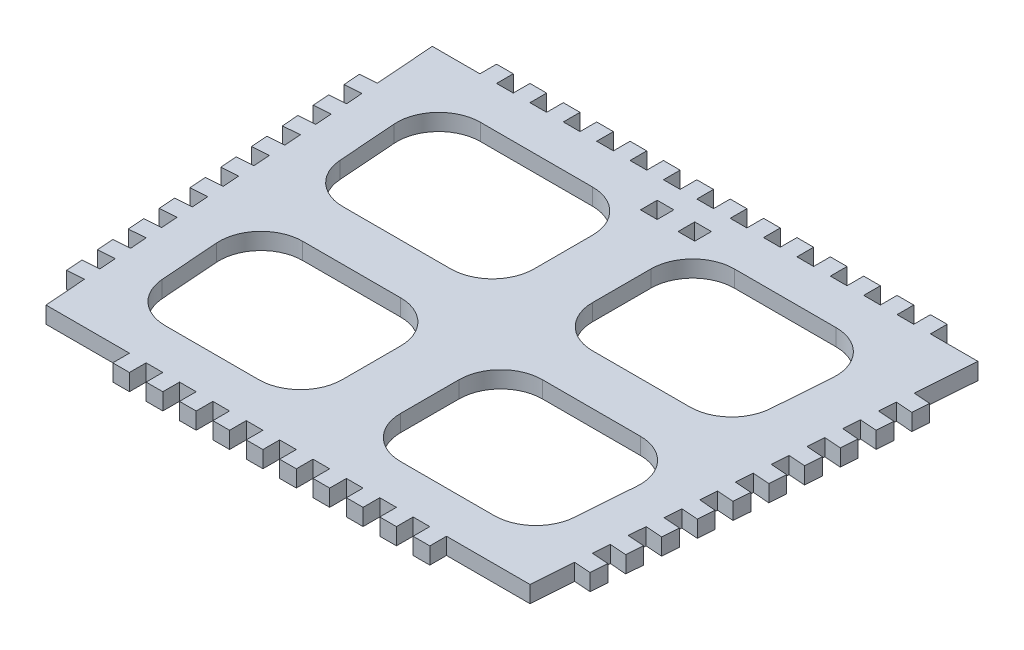
SolidWorks part; units mm, degrees
material "Cedar"
ref_plane "Front Plane" through (0, 0, 0) normal (0, 0, 1) x (1, 0, 0)
ref_plane "Top Plane" through (0, 0, 0) normal (0, 1, 0) x (1, 0, 0)
ref_plane "Right Plane" through (0, 0, 0) normal (1, 0, 0) x (0, 0, -1)
sketch "Sketch1" plane through (0, 0, 0) normal (0, 1, 0) x (1, 0, 0)
  line L0 (-65.4, 43.0243) -> (0, 43.0243)
  line L1 (65.4, 43.0243) -> (58, -56.9757)
  line L2 (58, -56.9757) -> (0, -56.9757)
  line L3 (-58, -56.9757) -> (-65.4, 43.0243)
  line L4 (0, 43.0243) -> (0, -56.9757) construction
  line L5 (0, -6.9757) -> (15.9946, -6.9757) construction
  line L48 (0, -56.9757) -> (-58, -56.9757)
  line L49 (0, 43.0243) -> (65.4, 43.0243)
  dimension "D1" = 100
  dimension "D2" = 65.4
  dimension "D3" = 58
  dimension "D14" = 65.4
  dimension "D15" = 58
extrude "Boss-Extrude1" add sketch "Sketch1" along normal blind 4
sketch "Sketch2" plane through (0, 4, 0) normal (0, 1, 0) x (1, 0, 0)
  line L0 (-65.4, 43.0243) -> (0, 43.0243) construction
  line L1 (-2, 43.0243) -> (-6, 43.0243)
  line L2 (-2, 43.0243) -> (-2, 47.0243)
  line L3 (-2, 47.0243) -> (-6, 47.0243)
  line L4 (-6, 43.0243) -> (-6, 47.0243)
  line L5 (0, 43.0243) -> (0, -56.9757) construction
  line L6 (-10, 43.0243) -> (-14, 43.0243)
  line L7 (-10, 43.0243) -> (-10, 47.0243)
  line L8 (-10, 47.0243) -> (-14, 47.0243)
  line L9 (-14, 43.0243) -> (-14, 47.0243)
  line L10 (-18, 43.0243) -> (-22, 43.0243)
  line L11 (-18, 43.0243) -> (-18, 47.0243)
  line L12 (-18, 47.0243) -> (-22, 47.0243)
  line L13 (-22, 43.0243) -> (-22, 47.0243)
  line L14 (-26, 43.0243) -> (-30, 43.0243)
  line L15 (-26, 43.0243) -> (-26, 47.0243)
  line L16 (-26, 47.0243) -> (-30, 47.0243)
  line L17 (-30, 43.0243) -> (-30, 47.0243)
  line L18 (-34, 43.0243) -> (-38, 43.0243)
  line L19 (-34, 43.0243) -> (-34, 47.0243)
  line L20 (-34, 47.0243) -> (-38, 47.0243)
  line L21 (-38, 43.0243) -> (-38, 47.0243)
  line L22 (-42, 43.0243) -> (-46, 43.0243)
  line L23 (-42, 43.0243) -> (-42, 47.0243)
  line L24 (-42, 47.0243) -> (-46, 47.0243)
  line L25 (-46, 43.0243) -> (-46, 47.0243)
  line L26 (-50, 43.0243) -> (-54, 43.0243)
  line L27 (-50, 43.0243) -> (-50, 47.0243)
  line L28 (-50, 47.0243) -> (-54, 47.0243)
  line L29 (-54, 43.0243) -> (-54, 47.0243)
  line L30 (0, 43.0243) -> (0, 11.5799) construction
  line L31 (54, 43.0243) -> (54, 47.0243)
  line L32 (50, 47.0243) -> (54, 47.0243)
  line L33 (50, 43.0243) -> (50, 47.0243)
  line L34 (50, 43.0243) -> (54, 43.0243)
  line L35 (46, 43.0243) -> (46, 47.0243)
  line L36 (42, 47.0243) -> (46, 47.0243)
  line L37 (42, 43.0243) -> (42, 47.0243)
  line L38 (42, 43.0243) -> (46, 43.0243)
  line L39 (38, 43.0243) -> (38, 47.0243)
  line L40 (34, 47.0243) -> (38, 47.0243)
  line L41 (34, 43.0243) -> (34, 47.0243)
  line L42 (34, 43.0243) -> (38, 43.0243)
  line L43 (30, 43.0243) -> (30, 47.0243)
  line L44 (26, 47.0243) -> (30, 47.0243)
  line L45 (26, 43.0243) -> (26, 47.0243)
  line L46 (26, 43.0243) -> (30, 43.0243)
  line L47 (22, 43.0243) -> (22, 47.0243)
  line L48 (18, 47.0243) -> (22, 47.0243)
  line L49 (18, 43.0243) -> (18, 47.0243)
  line L50 (18, 43.0243) -> (22, 43.0243)
  line L51 (14, 43.0243) -> (14, 47.0243)
  line L52 (10, 47.0243) -> (14, 47.0243)
  line L53 (10, 43.0243) -> (10, 47.0243)
  line L54 (10, 43.0243) -> (14, 43.0243)
  line L55 (6, 43.0243) -> (6, 47.0243)
  line L56 (2, 47.0243) -> (6, 47.0243)
  line L57 (2, 43.0243) -> (2, 47.0243)
  line L58 (2, 43.0243) -> (6, 43.0243)
  line L59 (0, -56.9757) -> (-58, -56.9757) construction
  line L60 (-6, -56.9757) -> (-2, -56.9757)
  line L61 (-6, -56.9757) -> (-6, -60.9757)
  line L62 (-6, -60.9757) -> (-2, -60.9757)
  line L63 (-2, -56.9757) -> (-2, -60.9757)
  line L64 (-14, -56.9757) -> (-10, -56.9757)
  line L65 (-14, -56.9757) -> (-14, -60.9757)
  line L66 (-14, -60.9757) -> (-10, -60.9757)
  line L67 (-10, -56.9757) -> (-10, -60.9757)
  line L68 (-22, -56.9757) -> (-18, -56.9757)
  line L69 (-22, -56.9757) -> (-22, -60.9757)
  line L70 (-22, -60.9757) -> (-18, -60.9757)
  line L71 (-18, -56.9757) -> (-18, -60.9757)
  line L72 (-30, -56.9757) -> (-26, -56.9757)
  line L73 (-30, -56.9757) -> (-30, -60.9757)
  line L74 (-30, -60.9757) -> (-26, -60.9757)
  line L75 (-26, -56.9757) -> (-26, -60.9757)
  line L76 (-38, -56.9757) -> (-34, -56.9757)
  line L77 (-38, -56.9757) -> (-38, -60.9757)
  line L78 (-38, -60.9757) -> (-34, -60.9757)
  line L79 (-34, -56.9757) -> (-34, -60.9757)
  line L80 (34, -56.9757) -> (34, -60.9757)
  line L81 (38, -60.9757) -> (34, -60.9757)
  line L82 (38, -56.9757) -> (38, -60.9757)
  line L83 (38, -56.9757) -> (34, -56.9757)
  line L84 (26, -56.9757) -> (26, -60.9757)
  line L85 (30, -60.9757) -> (26, -60.9757)
  line L86 (30, -56.9757) -> (30, -60.9757)
  line L87 (30, -56.9757) -> (26, -56.9757)
  line L88 (18, -56.9757) -> (18, -60.9757)
  line L89 (22, -60.9757) -> (18, -60.9757)
  line L90 (22, -56.9757) -> (22, -60.9757)
  line L91 (22, -56.9757) -> (18, -56.9757)
  line L92 (10, -56.9757) -> (10, -60.9757)
  line L93 (14, -60.9757) -> (10, -60.9757)
  line L94 (14, -56.9757) -> (14, -60.9757)
  line L95 (14, -56.9757) -> (10, -56.9757)
  line L96 (2, -56.9757) -> (2, -60.9757)
  line L97 (6, -60.9757) -> (2, -60.9757)
  line L98 (6, -56.9757) -> (6, -60.9757)
  line L99 (6, -56.9757) -> (2, -56.9757)
  dimension "D1" = 4
  dimension "D2" = 2
  dimension "D3" = 4
  dimension "D4" = 2
  dimension "D5" = 4
  dimension "D6" = 4
extrude "Boss-Extrude2" add sketch "Sketch2" against normal blind 4
sketch "Sketch4" plane through (0, 4, 0) normal (0, 1, 0) x (1, 0, 0)
  line L0 (-53.838, 22.2864) -> (-52.802, 8.2864)
  line L1 (-42.8293, -0.9757) -> (-17, -0.9757)
  line L2 (-7, 9.0243) -> (-7, 23.0243)
  line L3 (-17, 33.0243) -> (-43.8653, 33.0243)
  line L5 (-58, -56.9757) -> (-65.4, 43.0243) construction
  line L6 (0, -56.9757) -> (-58, -56.9757) construction
  line L7 (-65.4, 43.0243) -> (0, 43.0243) construction
  line L8 (0, 43.0243) -> (0, -56.9757) construction
  line L9 (0, 43.0243) -> (65.4, 43.0243) construction
  line L10 (7, 23.0243) -> (7, 9.0243)
  line L11 (-6.5, 38.0243) -> (-2.5, 38.0243)
  line L12 (17, -0.9757) -> (40.3576, -0.9757)
  line L13 (50.3304, 8.2864) -> (51.3664, 22.2864)
  line L14 (41.3936, 33.0243) -> (17, 33.0243)
  line L15 (65.4, 43.0243) -> (58, -56.9757) construction
  line L16 (0, -6.9757) -> (15.9946, -6.9757) construction
  line L17 (0, -6.9757) -> (17.2564, -6.9757) construction
  line L18 (-50.434, -23.7136) -> (-49.398, -37.7136)
  line L19 (-39.4253, -46.9757) -> (-17, -46.9757)
  line L20 (-7, -36.9757) -> (-7, -22.9757)
  line L21 (-17, -12.9757) -> (-40.4613, -12.9757)
  line L22 (7, -22.9757) -> (7, -36.9757)
  line L23 (17, -46.9757) -> (39.4253, -46.9757)
  line L24 (49.398, -37.7136) -> (50.434, -23.7136)
  line L25 (40.4613, -12.9757) -> (17, -12.9757)
  line L26 (-6.5, 38.0243) -> (-6.5, 34.0243)
  line L27 (-6.5, 34.0243) -> (-2.5, 34.0243)
  line L28 (-2.5, 38.0243) -> (-2.5, 34.0243)
  line L29 (2.5, 38.0243) -> (6.5, 38.0243)
  line L30 (2.5, 38.0243) -> (2.5, 34.0243)
  line L31 (2.5, 34.0243) -> (6.5, 34.0243)
  line L32 (6.5, 38.0243) -> (6.5, 34.0243)
  arc A0 (-52.802, 8.2864) -> (-42.8293, -0.9757) centre (-42.8293, 9.0243) ccw
  arc A1 (-17, -0.9757) -> (-7, 9.0243) centre (-17, 9.0243) ccw
  arc A2 (-7, 23.0243) -> (-17, 33.0243) centre (-17, 23.0243) ccw
  arc A3 (-53.838, 22.2864) -> (-43.8653, 33.0243) centre (-43.8653, 23.0243) cw
  arc A4 (7, 9.0243) -> (17, -0.9757) centre (17, 9.0243) ccw
  arc A5 (40.3576, -0.9757) -> (50.3304, 8.2864) centre (40.3576, 9.0243) ccw
  arc A6 (51.3664, 22.2864) -> (41.3936, 33.0243) centre (41.3936, 23.0243) ccw
  arc A7 (7, 23.0243) -> (17, 33.0243) centre (17, 23.0243) cw
  arc A8 (-49.398, -37.7136) -> (-39.4253, -46.9757) centre (-39.4253, -36.9757) ccw
  arc A9 (-17, -46.9757) -> (-7, -36.9757) centre (-17, -36.9757) ccw
  arc A10 (-7, -22.9757) -> (-17, -12.9757) centre (-17, -22.9757) ccw
  arc A11 (-50.434, -23.7136) -> (-40.4613, -12.9757) centre (-40.4613, -22.9757) cw
  arc A12 (7, -36.9757) -> (17, -46.9757) centre (17, -36.9757) ccw
  arc A13 (39.4253, -46.9757) -> (49.398, -37.7136) centre (39.4253, -36.9757) ccw
  arc A14 (50.434, -23.7136) -> (40.4613, -12.9757) centre (40.4613, -22.9757) ccw
  arc A15 (7, -22.9757) -> (17, -12.9757) centre (17, -22.9757) cw
  dimension "D1" = 10
  dimension "D5" = 10
  dimension "D6" = 10
  dimension "D8" = 10
  dimension "D10" = 10
  dimension "D2" = 6
  dimension "D3" = 7
  dimension "D4" = 10
  dimension "D7" = 10
  dimension "D9" = 7
  dimension "D11" = 10
  dimension "D12" = 7
  dimension "D13" = 7
  dimension "D14" = 10
  dimension "D15" = 6
  dimension "D16" = 10
  dimension "D17" = 4
  dimension "D18" = 4
  dimension "D19" = 2.5
  dimension "D20" = 4
  dimension "D21" = 4
  dimension "D22" = 2.5
  dimension "D23" = 5
extrude "Cut-Extrude1" cut sketch "Sketch4" against normal blind 10
sketch "Sketch5" plane through (0, 4, 0) normal (0, 1, 0) x (1, 0, 0)
  line L0 (-65.4, 43.0243) -> (-58, -56.9757) construction
  line L1 (-61.7, -6.9757) -> (61.7, -6.9757) construction
  line L2 (65.4, 43.0243) -> (58, -56.9757) construction
  line L3 (0, -6.9757) -> (0, -56.9757) construction
  line L4 (-59.6236, -35.0357) -> (-63.6127, -35.3308)
  line L5 (-63.6127, -35.3308) -> (-63.3175, -39.3199)
  line L6 (-63.3175, -39.3199) -> (-59.3284, -39.0247)
  line L7 (-59.3284, -39.0247) -> (-59.6236, -35.0357)
  line L8 (-61.7, -6.9757) -> (-78.3114, -8.2049) construction
  line L9 (-59.0332, -43.0138) -> (-63.0223, -43.309)
  line L10 (-63.0223, -43.309) -> (-62.7271, -47.2981)
  line L11 (-62.7271, -47.2981) -> (-58.738, -47.0029)
  line L12 (-58.738, -47.0029) -> (-59.0332, -43.0138)
  line L13 (-60.2139, -27.0575) -> (-64.203, -27.3527)
  line L14 (-64.203, -27.3527) -> (-63.9078, -31.3418)
  line L15 (-63.9078, -31.3418) -> (-59.9188, -31.0466)
  line L16 (-59.9188, -31.0466) -> (-60.2139, -27.0575)
  line L17 (-60.8043, -19.0793) -> (-64.7934, -19.3745)
  line L18 (-64.7934, -19.3745) -> (-64.4982, -23.3636)
  line L19 (-64.4982, -23.3636) -> (-60.5091, -23.0684)
  line L20 (-60.5091, -23.0684) -> (-60.8043, -19.0793)
  line L21 (-61.3947, -11.1011) -> (-65.3838, -11.3963)
  line L22 (-65.3838, -11.3963) -> (-65.0886, -15.3854)
  line L23 (-65.0886, -15.3854) -> (-61.0995, -15.0902)
  line L24 (-61.0995, -15.0902) -> (-61.3947, -11.1011)
  line L25 (-61.9851, -3.1229) -> (-65.9742, -3.4181)
  line L26 (-65.9742, -3.4181) -> (-65.679, -7.4072)
  line L27 (-65.679, -7.4072) -> (-61.6899, -7.112)
  line L28 (-61.6899, -7.112) -> (-61.9851, -3.1229)
  line L29 (-62.5755, 4.8553) -> (-66.5646, 4.5601)
  line L30 (-66.5646, 4.5601) -> (-66.2694, 0.571)
  line L31 (-66.2694, 0.571) -> (-62.2803, 0.8662)
  line L32 (-62.2803, 0.8662) -> (-62.5755, 4.8553)
  line L33 (-63.1659, 12.8335) -> (-67.155, 12.5383)
  line L34 (-67.155, 12.5383) -> (-66.8598, 8.5492)
  line L35 (-66.8598, 8.5492) -> (-62.8707, 8.8444)
  line L36 (-62.8707, 8.8444) -> (-63.1659, 12.8335)
  line L37 (-63.7563, 20.8116) -> (-67.7454, 20.5165)
  line L38 (-67.7454, 20.5165) -> (-67.4502, 16.5274)
  line L39 (-67.4502, 16.5274) -> (-63.4611, 16.8226)
  line L40 (-63.4611, 16.8226) -> (-63.7563, 20.8116)
  line L41 (-64.3466, 28.7898) -> (-68.3357, 28.4946)
  line L42 (-68.3357, 28.4946) -> (-68.0405, 24.5055)
  line L43 (-68.0405, 24.5055) -> (-64.0515, 24.8007)
  line L44 (-64.0515, 24.8007) -> (-64.3466, 28.7898)
  line L45 (64.0515, 24.8007) -> (64.3466, 28.7898)
  line L46 (68.0405, 24.5055) -> (64.0515, 24.8007)
  line L47 (68.3357, 28.4946) -> (68.0405, 24.5055)
  line L48 (64.3466, 28.7898) -> (68.3357, 28.4946)
  line L49 (63.4611, 16.8226) -> (63.7563, 20.8116)
  line L50 (67.4502, 16.5274) -> (63.4611, 16.8226)
  line L51 (67.7454, 20.5165) -> (67.4502, 16.5274)
  line L52 (63.7563, 20.8116) -> (67.7454, 20.5165)
  line L53 (62.8707, 8.8444) -> (63.1659, 12.8335)
  line L54 (66.8598, 8.5492) -> (62.8707, 8.8444)
  line L55 (67.155, 12.5383) -> (66.8598, 8.5492)
  line L56 (63.1659, 12.8335) -> (67.155, 12.5383)
  line L57 (62.2803, 0.8662) -> (62.5755, 4.8553)
  line L58 (66.2694, 0.571) -> (62.2803, 0.8662)
  line L59 (66.5646, 4.5601) -> (66.2694, 0.571)
  line L60 (62.5755, 4.8553) -> (66.5646, 4.5601)
  line L61 (61.6899, -7.112) -> (61.9851, -3.1229)
  line L62 (65.679, -7.4072) -> (61.6899, -7.112)
  line L63 (65.9742, -3.4181) -> (65.679, -7.4072)
  line L64 (61.9851, -3.1229) -> (65.9742, -3.4181)
  line L65 (61.0995, -15.0902) -> (61.3947, -11.1011)
  line L66 (65.0886, -15.3854) -> (61.0995, -15.0902)
  line L67 (65.3838, -11.3963) -> (65.0886, -15.3854)
  line L68 (61.3947, -11.1011) -> (65.3838, -11.3963)
  line L69 (60.5091, -23.0684) -> (60.8043, -19.0793)
  line L70 (64.4982, -23.3636) -> (60.5091, -23.0684)
  line L71 (64.7934, -19.3745) -> (64.4982, -23.3636)
  line L72 (60.8043, -19.0793) -> (64.7934, -19.3745)
  line L73 (59.9188, -31.0466) -> (60.2139, -27.0575)
  line L74 (63.9078, -31.3418) -> (59.9188, -31.0466)
  line L75 (64.203, -27.3527) -> (63.9078, -31.3418)
  line L76 (60.2139, -27.0575) -> (64.203, -27.3527)
  line L77 (58.738, -47.0029) -> (59.0332, -43.0138)
  line L78 (62.7271, -47.2981) -> (58.738, -47.0029)
  line L79 (63.0223, -43.309) -> (62.7271, -47.2981)
  line L80 (59.0332, -43.0138) -> (63.0223, -43.309)
  line L81 (59.3284, -39.0247) -> (59.6236, -35.0357)
  line L82 (63.3175, -39.3199) -> (59.3284, -39.0247)
  line L83 (63.6127, -35.3308) -> (63.3175, -39.3199)
  line L84 (59.6236, -35.0357) -> (63.6127, -35.3308)
  dimension "D1" = 10
  dimension "D2" = 4
  dimension "D5" = 10
extrude "Boss-Extrude3" add sketch "Sketch5" against normal blind 4
